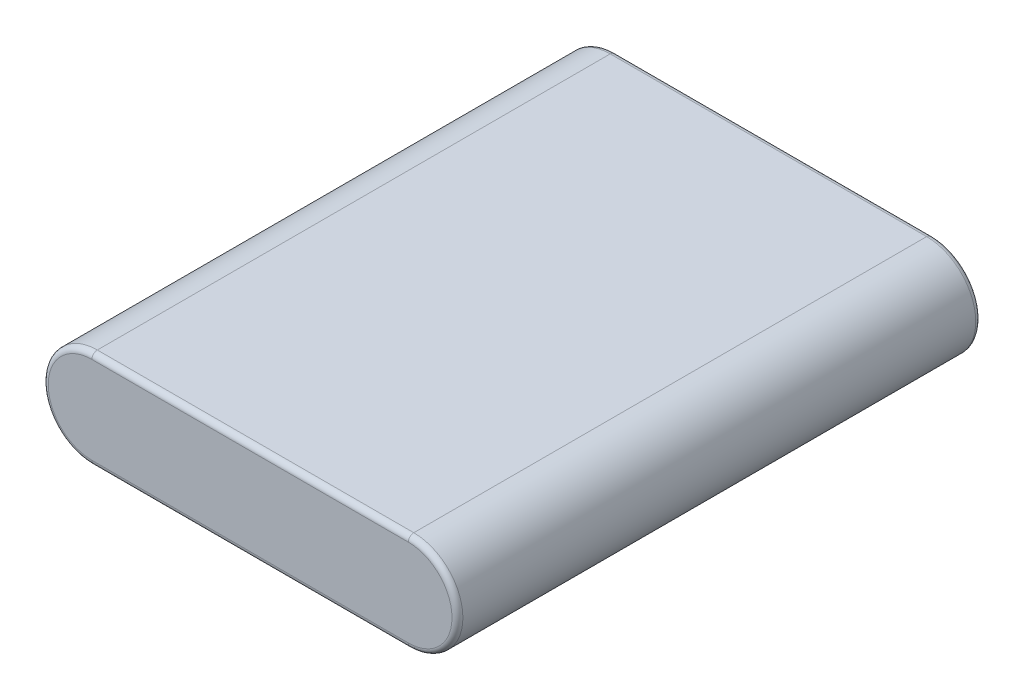
SolidWorks part; units mm, degrees
material "ABS"
ref_plane "Plan de face" through (0, 0, 0) normal (0, 0, 1) x (1, 0, 0)
ref_plane "Plan de dessus" through (0, 0, 0) normal (0, 1, 0) x (1, 0, 0)
ref_plane "Plan de droite" through (0, 0, 0) normal (1, 0, 0) x (0, 0, -1)
sketch "Esquisse1" plane through (0, 0, 0) normal (0, 0, 1) x (1, 0, 0)
  line L0 (0, 0) -> (58, 0) construction
  line L1 (0, 9) -> (58, 9)
  line L2 (0, -9) -> (58, -9)
  arc A0 (0, 9) -> (0, -9) centre (0, 0) ccw
  arc A1 (58, -9) -> (58, 9) centre (58, 0) ccw
  point P3 (29, 0)
  point P8 (-9, 0)
  point P9 (67, 0)
  dimension "D1" = 76
  dimension "D2" = 18
extrude "Boss.-Extru.1" add sketch "Esquisse1" along normal blind 96
fillet "Congé1" radius 1 8 edges at (67, 0, 0) (29, -9, 0) (-9, 0, 0) (67, 0, 96) (29, -9, 96) (-9, 0, 96) (29, 9, 0) (29, 9, 96)
